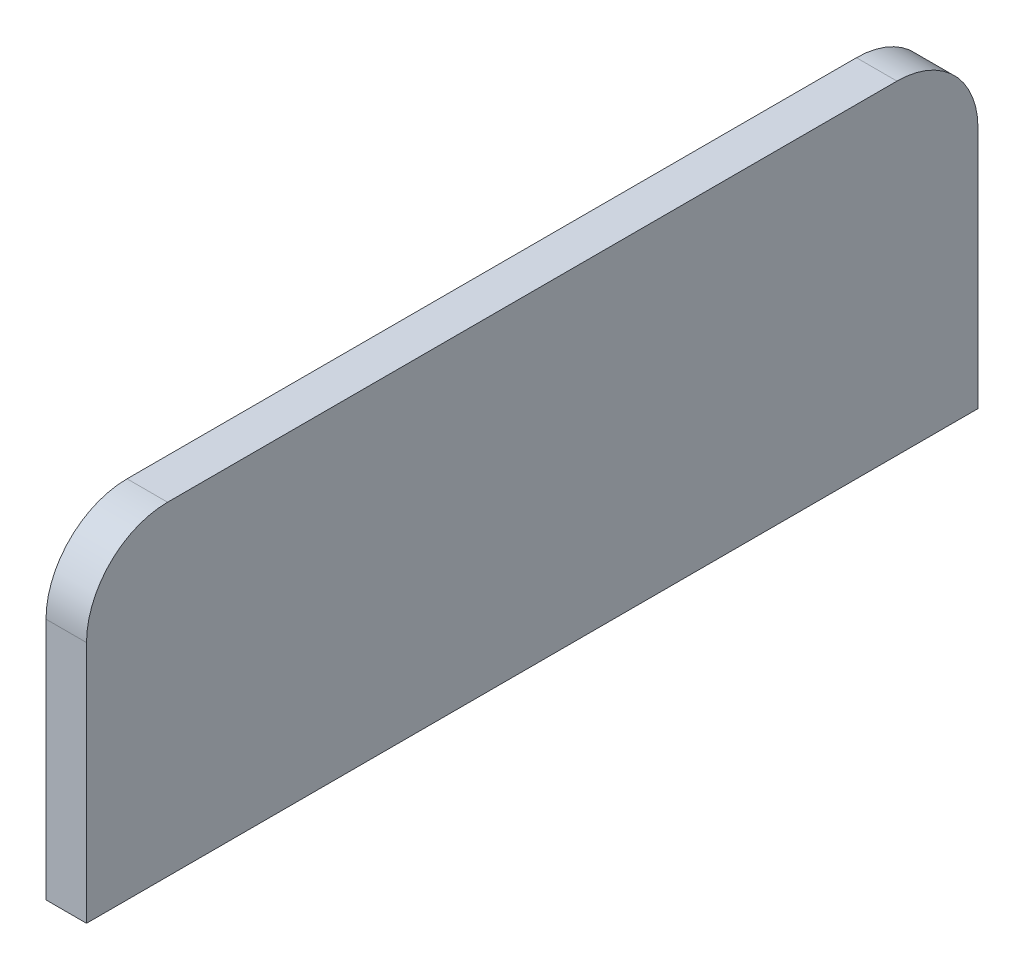
SolidWorks part; units mm, degrees
ref_plane "Front Plane" through (0, 0, 0) normal (0, 0, 1) x (1, 0, 0)
ref_plane "Top Plane" through (0, 0, 0) normal (0, 1, 0) x (1, 0, 0)
ref_plane "Right Plane" through (0, 0, 0) normal (1, 0, 0) x (0, 0, -1)
sketch "Sketch1" plane through (0, 0, 0) normal (1, 0, 0) x (0, 0, -1)
  line L1 (-34.925, 12.7) -> (34.925, 12.7)
  line L2 (-34.925, 12.7) -> (-34.925, -12.7)
  line L3 (-34.925, -12.7) -> (34.925, -12.7)
  line L4 (34.925, 12.7) -> (34.925, -12.7)
  line L5 (-34.925, 12.7) -> (34.925, -12.7) construction
  line L6 (-34.925, -12.7) -> (34.925, 12.7) construction
  point P0 (0, 0)
  dimension "D1" = 25.4
  dimension "D2" = 69.85
extrude "Boss-Extrude1" add sketch "Sketch1" along normal blind 3.175
fillet "Fillet1" radius 6.35 2 edges at (1.5875, 12.7, 34.925) (1.5875, 12.7, -34.925)
